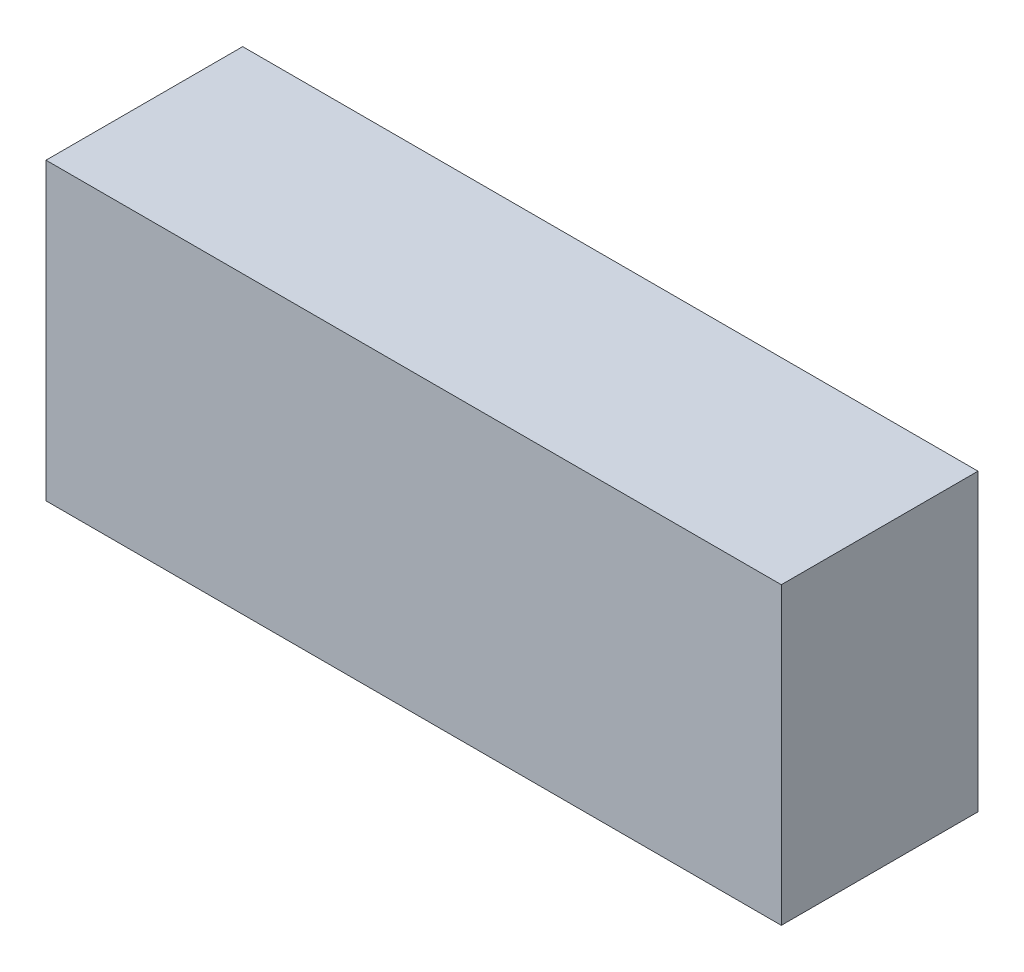
SolidWorks part; units mm, degrees
ref_plane "Front Plane" through (0, 0, 0) normal (0, 0, 1) x (1, 0, 0)
ref_plane "Top Plane" through (0, 0, 0) normal (0, 1, 0) x (1, 0, 0)
ref_plane "Right Plane" through (0, 0, 0) normal (1, 0, 0) x (0, 0, -1)
sketch "Sketch1" plane through (0, 0, 0) normal (0, 0, 1) x (1, 0, 0)
  line L1 (18.6929, -7.5) -> (-18.6929, -7.5)
  line L2 (18.6929, -7.5) -> (18.6929, 7.5)
  line L3 (18.6929, 7.5) -> (-18.6929, 7.5)
  line L4 (-18.6929, -7.5) -> (-18.6929, 7.5)
  line L5 (18.6929, -7.5) -> (-18.6929, 7.5) construction
  line L6 (18.6929, 7.5) -> (-18.6929, -7.5) construction
  point P0 (0, 0)
  dimension "D1" = 15
extrude "Extrude1" add sketch "Sketch1" along normal blind 10
